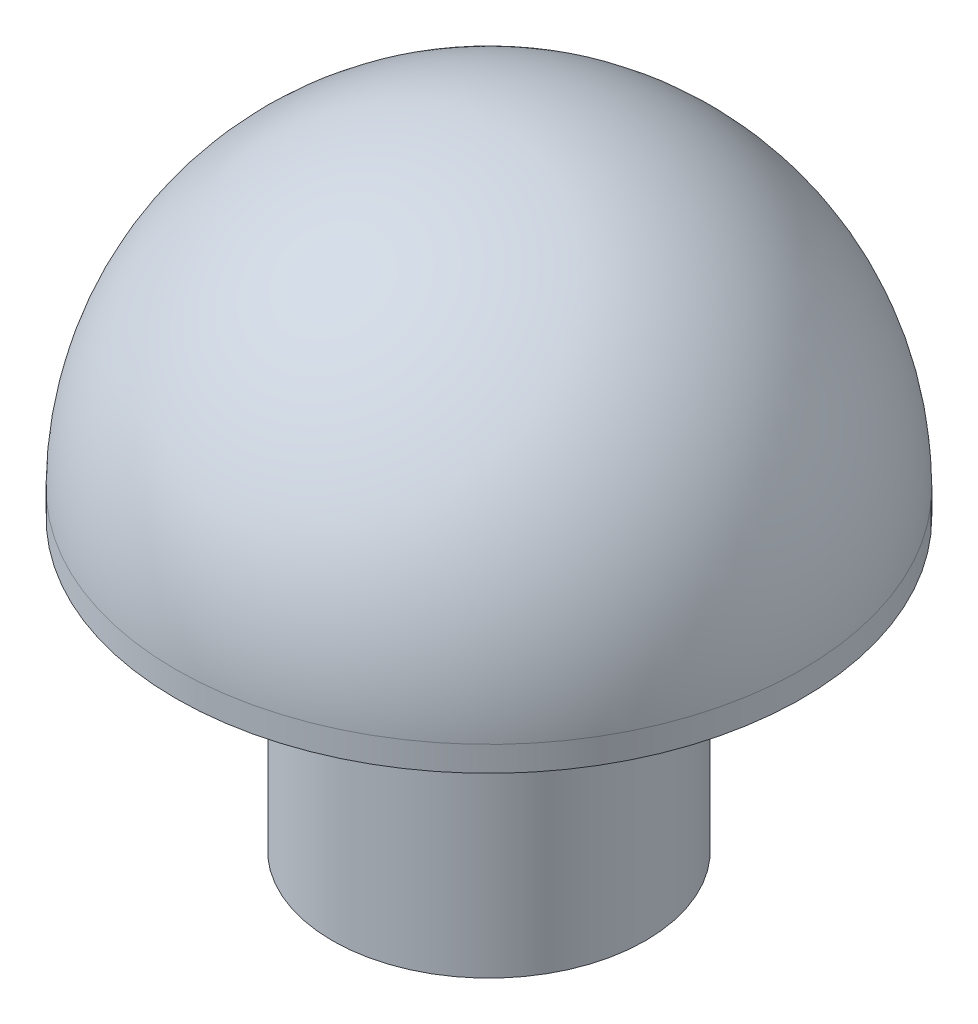
SolidWorks part; units mm, degrees
ref_plane "Front Plane" through (0, 0, 0) normal (0, 0, 1) x (1, 0, 0)
ref_plane "Top Plane" through (0, 0, 0) normal (0, 1, 0) x (1, 0, 0)
ref_plane "Right Plane" through (0, 0, 0) normal (1, 0, 0) x (0, 0, -1)
sketch "Sketch1" plane through (0, 0, 0) normal (0, 1, 0) x (1, 0, 0)
  circle A0 centre (0, 0) radius 2.5
  dimension "D1" = 5
extrude "Boss-Extrude1" add sketch "Sketch1" along normal blind 10
sketch "Sketch2" plane through (0, 10, 0) normal (0, 1, 0) x (1, 0, 0)
  circle A0 centre (0, 0) radius 5
  dimension "D1" = 10
extrude "Boss-Extrude2" add sketch "Sketch2" against normal blind 5.4
fillet "Fillet1" radius 5 1 edges at (0, 10, 5)
